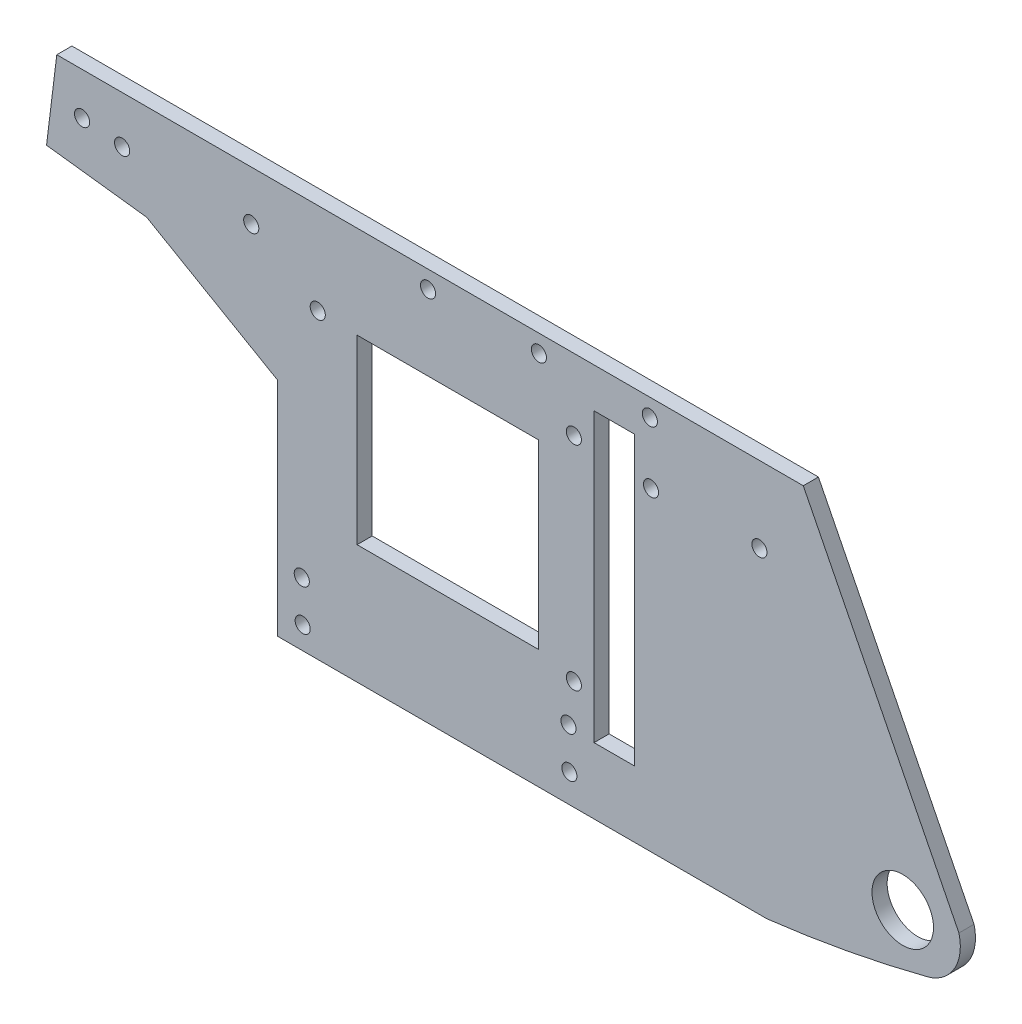
SolidWorks part; units mm, degrees
ref_plane "前视基准面" through (0, 0, 0) normal (0, 0, 1) x (1, 0, 0)
ref_plane "上视基准面" through (0, 0, 0) normal (0, 1, 0) x (1, 0, 0)
ref_plane "右视基准面" through (0, 0, 0) normal (1, 0, 0) x (0, 0, -1)
sketch "草图1" plane through (0, 0, 0) normal (0, 0, 1) x (1, 0, 0)
  line L0 (30.5874, 31.5554) -> (153.9483, 31.5554)
  line L2 (146.7554, -46.4446) -> (49.6754, -46.4446)
  line L5 (153.9483, 31.5554) -> (184.8227, -29.8383)
  line L6 (92.2678, 31.5554) -> (92.2678, -46.4446) construction
  line L7 (92.2678, -7.4446) -> (144.0701, -7.4446) construction
  line L8 (92.2678, -7.4446) -> (95.382, -7.4446) construction
  line L9 (95.382, -7.4446) -> (95.382, 6.5554) construction
  line L10 (95.382, 6.5554) -> (60.382, 6.5554) construction
  line L11 (60.382, 6.5554) -> (60.382, -21.4446) construction
  line L12 (60.382, -21.4446) -> (95.382, -21.4446) construction
  line L13 (95.382, -21.4446) -> (95.382, -7.4446) construction
  line L14 (23.6947, 12.5554) -> (49.6754, -2.4446)
  line L15 (49.6754, -2.4446) -> (49.6754, -46.4446)
  line L16 (23.6947, 12.5554) -> (3.8438, 14.9928)
  line L17 (3.8438, 14.9928) -> (5.8774, 31.5554)
  line L18 (5.8774, 31.5554) -> (30.5874, 31.5554)
  arc A4 (184.8227, -29.8383) -> (178.5401, -40.4962) centre (176.3658, -32.0339) cw
  arc A5 (178.5401, -40.4962) -> (146.7554, -46.4446) centre (117.9848, 195.1848) cw
  point P7 (181.997, -46.4446)
  point P14 (-18.003, -46.4446)
  point P17 (27.0303, 31.5554)
  dimension "D4" = 68.7198
  dimension "D5" = 8.7372
  dimension "D3" = 123.3609
  dimension "D6" = 157
  dimension "D11" = 243.3362
  dimension "D2" = 30
  dimension "160" = 200
  dimension "D7" = 78
  dimension "D8" = 35
  dimension "D9" = 14
  dimension "D10" = 14
  dimension "D12" = 116.697
  dimension "D13" = 97.08
  dimension "D14" = 44
  dimension "D15" = 120
  dimension "D16" = 20
  dimension "D17" = 24.71
extrude "凸台-拉伸1" add sketch "草图1" along normal blind 3
sketch "草图2" plane through (0, 0, 3) normal (0, 0, 1) x (1, 0, 0)
  line L0 (92.4143, -41.5608) -> (92.4143, 33.4392) construction
  line L5 (49.6754, -2.4446) -> (49.6754, -46.4446) construction
  line L6 (153.9483, 31.5554) -> (5.8774, 31.5554) construction
  line L7 (92.4143, -4.0608) -> (46.7593, -4.0608) construction
  line L26 (65.4399, 13.1727) -> (101.4399, 13.1727)
  line L32 (65.4399, 13.1727) -> (65.4399, -22.8273)
  line L33 (65.4399, -22.8273) -> (101.4399, -22.8273)
  line L34 (101.4399, 13.1727) -> (101.4399, -22.8273)
  line L35 (101.4399, -4.8273) -> (112.4399, -4.8273) construction
  line L36 (112.4399, -4.8273) -> (112.4399, -33.3273)
  line L37 (112.4399, -33.3273) -> (120.4399, -33.3273)
  line L38 (120.4399, -33.3273) -> (120.4399, 23.6727)
  line L39 (120.4399, 23.6727) -> (112.4399, 23.6727)
  line L40 (112.4399, 23.6727) -> (112.4399, -4.8273)
  circle A3 centre (173.6754, -31.4446) radius 6.1
  dimension "D6" = 12.2
  dimension "D7" = 124
  dimension "D8" = 63
  dimension "D1" = 36
  dimension "D2" = 36
  dimension "D3" = 11
  dimension "D4" = 57
  dimension "D5" = 8
extrude "切除-拉伸1" cut sketch "草图2" against normal up to next
hole_wizard "大小mm Clearance 暗销孔1" positions "草图4" profile "草图5" hole size "Ø3.0" standard "ISO" end condition through all
sketch "草图4" plane through (141.5106, 151.8592, 3) normal (0, 0, 1) x (-0.9998, -0.021, 0)
  point P0 (20.5912, 123.3982)
  point P2 (42.5912, 122.9368)
  point P4 (64.5816, 122.4756)
sketch "草图5" plane through (123.5113, 28.0564, 3) normal (1, 0, 0) x (0, -1, 0)
  line L0 (0, 0) -> (0, 3)
  line L1 (0, 3) -> (1.5, 3)
  line L2 (1.5, 3) -> (1.5, 0)
  line L3 (1.5, 0) -> (0, 0)
  line L4 (0, -6.35) -> (0, 107.95) construction
  dimension "通孔孔直径" = 3
  dimension "通孔孔深度" = 3
hole_wizard "大小mm Clearance 暗销孔4" positions "草图10" profile "草图11" hole size "Ø3.0" standard "ISO" end condition through all
sketch "草图10" plane through (141.5106, 151.8592, 3) normal (0, 0, 1) x (-0.9998, -0.021, 0)
  point P0 (20.6088, 135.4526)
  point P2 (-0.9003, 135.4526)
sketch "草图11" plane through (123.7465, 16.0043, 3) normal (1, 0, 0) x (0, -1, 0)
  line L0 (0, 0) -> (0, 3)
  line L1 (0, 3) -> (1.5, 3)
  line L2 (1.5, 3) -> (1.5, 0)
  line L3 (1.5, 0) -> (0, 0)
  line L4 (0, -6.35) -> (0, 107.95) construction
  dimension "通孔孔直径" = 3
  dimension "通孔孔深度" = 3
hole_wizard "大小mm Press 暗销孔1" positions "草图16" profile "草图17" hole size "Ø3.0" standard "ISO" end condition through all
sketch "草图16" plane through (141.6737, 151.8582, 3) normal (0, 0, 1) x (-0.9998, -0.021, 0)
  point P0 (36.0454, 133.7091)
  point P3 (36.0454, 133.7091)
  point P5 (36.9307, 175.9191)
sketch "草图17" plane through (108.4399, 17.4227, 3) normal (1, 0, 0) x (0, -1, 0)
  line L0 (0, 0) -> (0, 3)
  line L1 (0, 3) -> (1.5, 3)
  line L2 (1.5, 3) -> (1.5, 0)
  line L3 (1.5, 0) -> (0, 0)
  line L4 (0, -6.35) -> (0, 107.95) construction
  dimension "通孔孔直径" = 3
  dimension "通孔孔深度" = 3
hole_wizard "大小mm Press 暗销孔2" positions "草图20" profile "草图21" hole size "Ø3.0" standard "ISO" end condition through all
sketch "草图20" plane through (143.5473, 150.6254, 3) normal (0, 0, 1) x (-0.9998, -0.0223, 0)
  point P0 (88.939, 135.2274)
  point P2 (101.9425, 126.6475)
  point P4 (127.5376, 125.5988)
  point P7 (135.4543, 124.4474)
sketch "草图21" plane through (57.6396, 13.4523, 3) normal (1, 0, 0) x (0, -1, 0)
  line L0 (0, 0) -> (0, 3)
  line L1 (0, 3) -> (1.5, 3)
  line L2 (1.5, 3) -> (1.5, 0)
  line L3 (1.5, 0) -> (0, 0)
  line L4 (0, -6.35) -> (0, 107.95) construction
  dimension "通孔孔直径" = 3
  dimension "通孔孔深度" = 3
hole_wizard "大小mm Press 暗销孔4" positions "草图24" profile "草图25" hole size "Ø3.0" standard "ISO" end condition through all
sketch "草图24" plane through (143.5473, 150.6254, 3) normal (0, 0, 1) x (-0.9998, -0.0223, 0)
  point P0 (93.1614, 190.5782)
  point P2 (93.1614, 182.5471)
  point P4 (40.2454, 190.5782)
  point P5 (40.2454, 182.5471)
sketch "草图25" plane through (54.6499, -41.9788, 3) normal (1, 0, 0) x (0, -1, 0)
  line L0 (0, 0) -> (0, 3)
  line L1 (0, 3) -> (1.5, 3)
  line L2 (1.5, 3) -> (1.5, 0)
  line L3 (1.5, 0) -> (0, 0)
  line L4 (0, -6.35) -> (0, 107.95) construction
  dimension "通孔孔直径" = 3
  dimension "通孔孔深度" = 3
